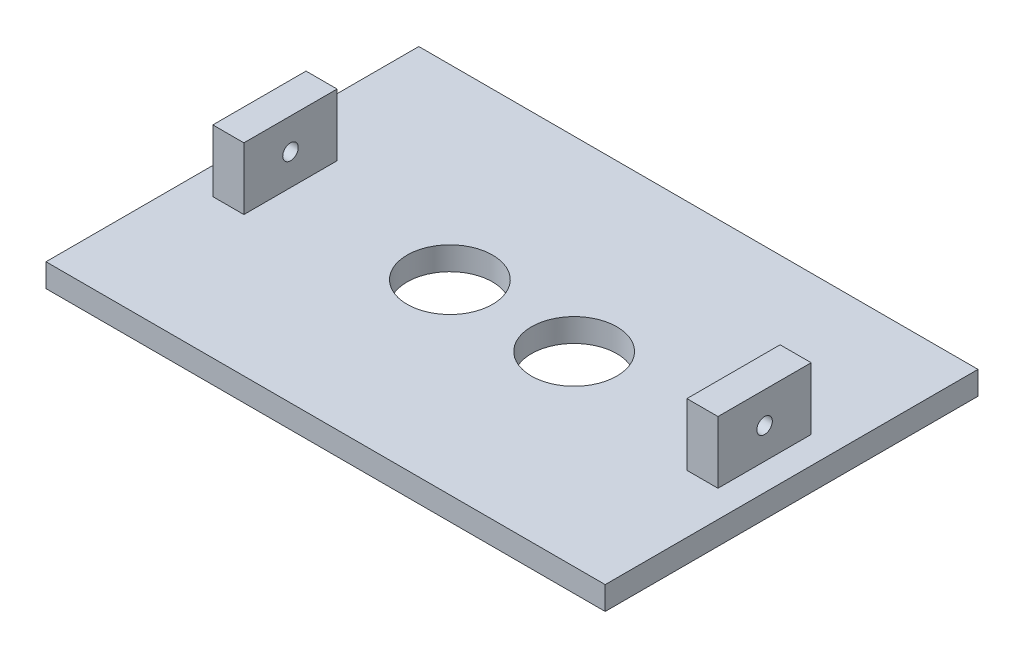
SolidWorks part; units mm, degrees
ref_plane "Front Plane" through (0, 0, 0) normal (0, 0, 1) x (1, 0, 0)
ref_plane "Top Plane" through (0, 0, 0) normal (0, 1, 0) x (1, 0, 0)
ref_plane "Right Plane" through (0, 0, 0) normal (1, 0, 0) x (0, 0, -1)
sketch "Sketch1" plane through (0, 0, 0) normal (0, 1, 0) x (1, 0, 0)
  line L1 (-57.15, 38.1) -> (57.15, 38.1)
  line L2 (-57.15, 38.1) -> (-57.15, -38.1)
  line L3 (-57.15, -38.1) -> (57.15, -38.1)
  line L4 (57.15, 38.1) -> (57.15, -38.1)
  line L5 (-57.15, 38.1) -> (57.15, -38.1) construction
  line L6 (-57.15, -38.1) -> (57.15, 38.1) construction
  point P0 (0, 0)
  dimension "D1" = 114.3
  dimension "D2" = 76.2
extrude "MainCover" add sketch "Sketch1" along normal blind 4.7625
sketch "Sketch2" plane through (0, 4.7625, 0) normal (0, 1, 0) x (1, 0, 0)
  line L0 (-57.15, 0) -> (-51.6255, 0) construction
  line L1 (-57.15, 38.1) -> (-57.15, -38.1) construction
  line L2 (-51.6255, 0) -> (51.6255, 0) construction
  line L3 (-45.2755, -9.525) -> (-51.6255, -9.525)
  line L4 (-45.2755, -9.525) -> (-45.2755, 9.525)
  line L5 (-45.2755, 9.525) -> (-51.6255, 9.525)
  line L6 (-51.6255, -9.525) -> (-51.6255, 9.525)
  line L7 (-45.2755, -9.525) -> (-51.6255, 9.525) construction
  line L8 (-45.2755, 9.525) -> (-51.6255, -9.525) construction
  line L9 (0, 0) -> (0, 18.4407) construction
  line L10 (45.2755, 9.525) -> (51.6255, -9.525) construction
  line L11 (45.2755, -9.525) -> (51.6255, 9.525) construction
  line L12 (57.15, 0) -> (51.6255, 0) construction
  line L13 (51.6255, -9.525) -> (51.6255, 9.525)
  line L14 (45.2755, 9.525) -> (51.6255, 9.525)
  line L15 (45.2755, -9.525) -> (45.2755, 9.525)
  line L16 (45.2755, -9.525) -> (51.6255, -9.525)
  point P5 (-48.4505, 0)
  point P18 (48.4505, 0)
  dimension "D1" = 5.5245
  dimension "D2" = 6.35
  dimension "D3" = 19.05
extrude "Boss-Extrude1" add sketch "Sketch2" along normal blind 12.7
sketch "Sketch3" plane through (-51.6255, 0, 0) normal (-1, 0, 0) x (0, 0, 1)
  line L0 (0, 4.7625) -> (0, 11.1125) construction
  line L1 (-9.525, 4.7625) -> (9.525, 4.7625) construction
  circle A0 centre (0, 11.1125) radius 1.5875
  dimension "D2" = 3.175
  dimension "D1" = 6.35
extrude "Cut-Extrude1" cut sketch "Sketch3" against normal through all both and the other way through all
sketch "Sketch4" plane through (0, 0, 0) normal (0, -1, 0) x (1, 0, 0)
  line L0 (0, 0) -> (12.7, 0) construction
  line L1 (0, 0) -> (0, -7.2487) construction
  circle A0 centre (12.7, 0) radius 8.7312
  circle A1 centre (-12.7, 0) radius 8.7312
  dimension "D1" = 17.4625
  dimension "D2" = 25.4
extrude "Cut-Extrude2" cut sketch "Sketch4" against normal through all
